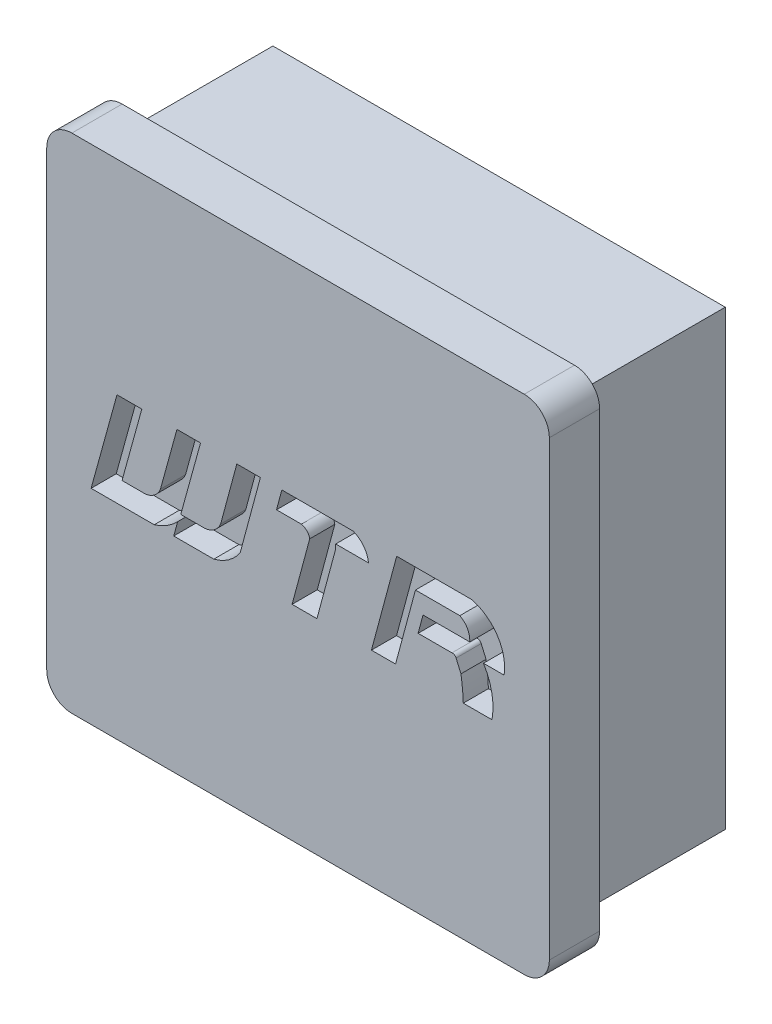
SolidWorks part; units mm, degrees
ref_plane "前视基准面" through (0, 0, 0) normal (0, 0, 1) x (1, 0, 0)
ref_plane "上视基准面" through (0, 0, 0) normal (0, 1, 0) x (1, 0, 0)
ref_plane "右视基准面" through (0, 0, 0) normal (1, 0, 0) x (0, 0, -1)
sketch "草图1" plane through (0, 0, 0) normal (0, 0, 1) x (1, 0, 0)
  line L1 (-9, -9) -> (9, -9)
  line L2 (-9, -9) -> (-9, 9)
  line L3 (-9, 9) -> (9, 9)
  line L4 (9, -9) -> (9, 9)
  line L5 (-9, -9) -> (9, 9) construction
  line L6 (-9, 9) -> (9, -9) construction
  point P0 (0, 0)
  dimension "D1" = 18
  dimension "D2" = 18
extrude "凸台-拉伸1" add sketch "草图1" along normal blind 6
sketch "草图3" plane through (0, 0, 6) normal (0, 0, 1) x (1, 0, 0)
  line L1 (-10, -10) -> (10, -10)
  line L2 (-10, -10) -> (-10, 10)
  line L3 (-10, 10) -> (10, 10)
  line L4 (10, -10) -> (10, 10)
  line L5 (-10, -10) -> (10, 10) construction
  line L6 (-10, 10) -> (10, -10) construction
  point P0 (0, 0)
  dimension "D1" = 20
  dimension "D2" = 20
extrude "凸台-拉伸2" add sketch "草图3" along normal blind 2
fillet "圆角1" radius 1 4 edges at (10, -10, 7) (-10, -10, 7) (-10, 10, 7) (10, 10, 7)
sketch "草图5" plane through (0, 0, 8) normal (0, 0, 1) x (1, 0, 0)
  line L0 (-7.2046, 1.8794) -> (-8.2345, -1.8595)
  line L1 (-8.2345, -1.8595) -> (-5.7231, -1.8595)
  line L2 (-4.9471, -1.8595) -> (-3.3528, -1.8595)
  line L3 (-7.2046, 1.8794) -> (-6.2169, 1.8794)
  line L4 (-6.2169, 1.8794) -> (-7.0035, -0.976)
  line L5 (-7.0035, -0.976) -> (-6.054, -0.976)
  line L6 (-4.8187, 1.8794) -> (-5.4778, -0.5132)
  line L7 (-4.8187, 1.8794) -> (-3.8802, 1.8794)
  line L8 (-3.8802, 1.8794) -> (-4.6668, -0.976)
  line L9 (-4.6668, -0.976) -> (-3.6964, -0.976)
  line L10 (-2.4363, 1.8794) -> (-3.0795, -0.5132)
  line L11 (-2.4363, 1.8794) -> (-1.4978, 1.8794)
  line L12 (-1.4978, 1.8794) -> (-2.3036, -1.1181)
  line L13 (-0.8571, 1.0889) -> (-0.6446, 1.8794)
  line L14 (-0.6446, 1.8794) -> (2.1962, 1.8794)
  line L15 (-0.8571, 1.0889) -> (0.1305, 1.0889)
  line L16 (1.4986, 1.0889) -> (2.8033, 1.0889)
  line L17 (-0.237, -1.8595) -> (0.464, 0.748)
  line L18 (-0.237, -1.8595) -> (0.7513, -1.8595)
  line L19 (0.7513, -1.8595) -> (1.4986, 0.9201)
  line L20 (1.4986, 1.0889) -> (1.4986, 0.9201)
  line L21 (3.925, 1.8794) -> (2.9199, -1.8595)
  line L22 (2.9199, -1.8595) -> (3.8798, -1.8595)
  line L23 (3.8798, -1.8595) -> (4.6724, 1.0889)
  line L24 (4.6724, 1.0889) -> (6.4392, 1.0889)
  line L25 (3.925, 1.8794) -> (6.9178, 1.8794)
  line L26 (7.3784, -0.0813) -> (8.1998, -0.0813)
  line L27 (6.8314, 0.3793) -> (4.9733, 0.3793)
  line L28 (4.9733, 0.3793) -> (4.7771, -0.3507)
  line L29 (4.7771, -0.3507) -> (6.1233, -0.3507)
  line L30 (6.2887, -0.4483) -> (6.482, -0.8948)
  line L31 (6.575, -1.8595) -> (7.7174, -1.8595)
  line L32 (-4.9471, -1.8595) -> (-4.7886, -1.2842)
  arc A0 (-6.054, -0.976) -> (-5.4778, -0.5132) centre (-6.1733, -0.2375) ccw
  arc A1 (-3.6964, -0.976) -> (-3.0795, -0.5132) centre (-3.7848, -0.2156) ccw
  arc A2 (0.1305, 1.0889) -> (0.464, 0.748) centre (0.0517, 0.6782) cw
  arc A3 (2.1962, 1.8794) -> (2.8033, 1.0889) centre (1.8639, 0.9959) cw
  arc A4 (6.482, -0.8948) -> (6.575, -1.8595) centre (-1.2835, -2.1302) cw
  arc A5 (7.7174, -1.8595) -> (7.3784, -0.0813) centre (5.2297, -1.4123) ccw
  arc A6 (6.2887, -0.4483) -> (6.1233, -0.3507) centre (6.139, -0.5132) ccw
  arc A7 (6.9178, 1.8794) -> (8.1998, -0.0813) centre (6.4689, 0.1864) cw
  arc A8 (-3.3528, -1.8595) -> (-2.3036, -1.1181) centre (-3.8012, -0.1118) ccw
  arc A9 (-5.7231, -1.8595) -> (-4.7886, -1.2842) centre (-6.3458, 0.1984) ccw
  arc A10 (6.8314, 0.3793) -> (6.4392, 1.0889) centre (6.0983, 0.4372) ccw
extrude "切除-拉伸2" cut sketch "草图5" against normal blind 1
